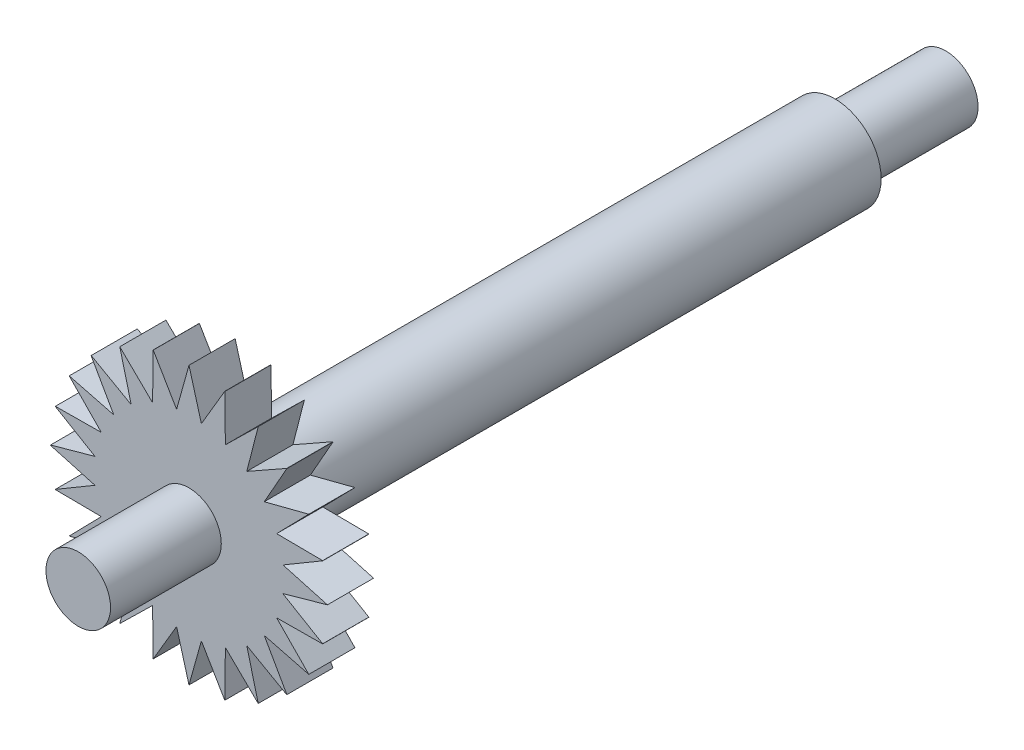
SolidWorks part; units mm, degrees
ref_plane "Plan de face" through (0, 0, 0) normal (0, 0, 1) x (1, 0, 0)
ref_plane "Plan de dessus" through (0, 0, 0) normal (0, 1, 0) x (1, 0, 0)
ref_plane "Plan de droite" through (0, 0, 0) normal (1, 0, 0) x (0, 0, -1)
sketch "Esquisse1" plane through (0, 0, 0) normal (0, 0, 1) x (1, 0, 0)
  circle A0 centre (0, 0) radius 5
  dimension "D1" = 10
extrude "Boss.-Extru.2" add sketch "Esquisse1" along normal blind 70
sketch "Esquisse2" plane through (0, 0, 0) normal (0, 0, -1) x (-1, 0, 0)
  circle A0 centre (0, 0) radius 3.5
  dimension "D1" = 7
extrude "Boss.-Extru.3" add sketch "Esquisse2" along normal blind 12
sketch "Esquisse4" plane through (0, 0, 70) normal (0, 0, 1) x (1, 0, 0)
  circle A0 centre (0, 0) radius 15
  dimension "D1" = 30
extrude "Boss.-Extru.5" add sketch "Esquisse4" against normal blind 5
sketch "Esquisse5" plane through (0, 0, 70) normal (0, 0, 1) x (1, 0, 0)
  circle A0 centre (0, 0) radius 3.5
  dimension "D1" = 7
extrude "Boss.-Extru.6" add sketch "Esquisse5" along normal blind 12
sketch "Esquisse6" plane through (0, 0, 70) normal (0, 0, 1) x (1, 0, 0)
  line L0 (0, 10) -> (0, -10) construction
  line L1 (-10, 0) -> (10, 0) construction
  line L2 (0, 10) -> (0, 15) construction
  line L3 (10, 0) -> (15, 0) construction
  line L4 (15, 0) -> (-15, 0) construction
  line L5 (0, -10) -> (0, -15) construction
  line L6 (0, 15) -> (1.425, 9.8979)
  line L7 (0, 15) -> (-1.425, 9.8979)
  line L8 (0, 0) -> (-3.8907, 14.5215) construction
  line L9 (0, 0) -> (-7.5126, 13.022) construction
  line L10 (0, 0) -> (-10.6237, 10.6372) construction
  line L11 (0, 0) -> (-13.0125, 7.5291) construction
  line L12 (0, 0) -> (-14.5165, 3.9092) construction
  line L13 (-3.8907, 14.5215) -> (-1.1901, 9.9289)
  line L14 (-3.8907, 14.5215) -> (-3.9427, 9.19)
  line L15 (-7.4994, 12.9907) -> (-6.1827, 7.8596)
  line L16 (-7.4994, 12.9907) -> (-3.7145, 9.2845)
  line L17 (-14.5165, 3.9092) -> (-9.1849, 3.9543)
  line L18 (-14.5165, 3.9092) -> (-9.9274, 1.2028)
  line L19 (-10.6237, 10.6372) -> (-7.9997, 6.0004)
  line L20 (-10.6237, 10.6372) -> (-5.9821, 8.0134)
  line L21 (-12.9812, 7.516) -> (-7.8518, 6.1927)
  line L22 (-12.9812, 7.516) -> (-9.2798, 3.7263)
  line L23 (-15, 0.0191) -> (-9.8961, 1.4376)
  line L24 (-15, 0.0191) -> (-9.8998, -1.4124)
  line L25 (-15, -0.0191) -> (-9.8961, -1.4376)
  line L26 (-14.5165, -3.9092) -> (-9.9274, -1.2028)
  line L27 (-14.5165, -3.9092) -> (-9.1849, -3.9543)
  line L28 (-12.9812, -7.516) -> (-9.2798, -3.7263)
  line L29 (-12.9812, -7.516) -> (-7.8518, -6.1927)
  line L30 (-10.6237, -10.6372) -> (-7.9997, -6.0004)
  line L31 (-10.6237, -10.6372) -> (-5.9821, -8.0134)
  line L32 (-7.4994, -12.9907) -> (-6.1827, -7.8596)
  line L33 (-7.4994, -12.9907) -> (-3.7145, -9.2845)
  line L34 (-3.8907, -14.5215) -> (-3.9427, -9.19)
  line L35 (-3.8907, -14.5215) -> (-1.1901, -9.9289)
  line L36 (0, -15) -> (-1.425, -9.8979)
  line L37 (0, -15) -> (1.425, -9.8979)
  line L38 (3.8907, -14.5215) -> (1.1901, -9.9289)
  line L39 (3.8907, -14.5215) -> (3.9427, -9.19)
  line L40 (7.4994, -12.9907) -> (3.7145, -9.2845)
  line L41 (7.4994, -12.9907) -> (6.1827, -7.8596)
  line L42 (10.6237, -10.6372) -> (5.9821, -8.0134)
  line L43 (10.6237, -10.6372) -> (7.9997, -6.0004)
  line L44 (12.9812, -7.516) -> (7.8518, -6.1927)
  line L45 (12.9812, -7.516) -> (9.2798, -3.7263)
  line L46 (14.5165, -3.9092) -> (9.1849, -3.9543)
  line L47 (14.5165, -3.9092) -> (9.9274, -1.2028)
  line L48 (15, 0.0191) -> (9.8998, -1.4124)
  line L49 (15, 0.0191) -> (9.8961, 1.4376)
  line L50 (14.5165, 3.9092) -> (9.9274, 1.2028)
  line L51 (14.5165, 3.9092) -> (9.1849, 3.9543)
  line L52 (12.9812, 7.516) -> (9.2798, 3.7263)
  line L53 (12.9812, 7.516) -> (7.8518, 6.1927)
  line L54 (10.6237, 10.6372) -> (7.9997, 6.0004)
  line L55 (10.6237, 10.6372) -> (5.9821, 8.0134)
  line L56 (7.4994, 12.9907) -> (6.1827, 7.8596)
  line L57 (7.4994, 12.9907) -> (3.7145, 9.2845)
  line L58 (0, 15) -> (1.425, 9.8979)
  line L59 (3.8907, 14.5215) -> (3.9427, 9.19)
  line L60 (3.8907, 14.5215) -> (1.1901, 9.9289)
  circle A0 centre (0, 0) radius 10
  circle A1 centre (0, 0) radius 15 construction
  circle A2 centre (0, 0) radius 15.0337
  point P89 (-14.555, 11.2674)
  circle M35 centre (0, 0) radius 15
  dimension "D3" = 1.425
  dimension "D4" = 3.92
  dimension "D8" = 3.92
  dimension "D9" = 2.85
  dimension "D10" = 1.43
extrude "Enlèv. mat.-Extru.1" cut sketch "Esquisse6" against normal blind 12 contours L20 L15 M35 | L21 L19 M35 | L22 L17 M35 | L23 L18 M35 | L26 L25 M35 | L28 L27 M35 | L30 L29 M35 | L32 L31 M35 | L34 L33 M35 | L36 L35 M35 | L38 L37 M35 | L40 L39 M35 | L42 L41 M35 | L44 L43 M35 | L46 L45 M35 | L48 L47 M35 | L50 L49 M35 | L52 L51 M35 | L54 L53 M35 | L56 L55 M35 | L59 L57 M35 | L60 L6 M35 | L13 L7 M35 | L16 L14 M35
